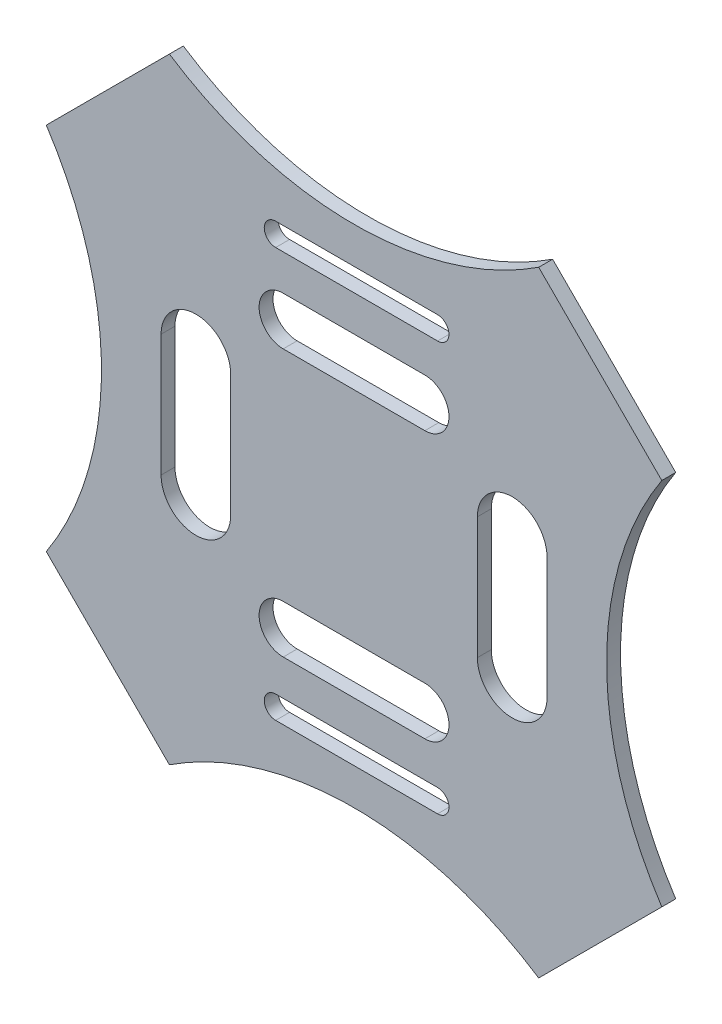
SolidWorks part; units mm, degrees
material "A-Glass Fiber"
ref_plane "Front Plane" through (0, 0, 0) normal (0, 0, 1) x (1, 0, 0)
ref_plane "Top Plane" through (0, 0, 0) normal (0, 1, 0) x (1, 0, 0)
ref_plane "Right Plane" through (0, 0, 0) normal (1, 0, 0) x (0, 0, -1)
sketch "Sketch1" plane through (0, 0, 0) normal (0, 0, 1) x (1, 0, 0)
  line L0 (-26.5165, 44.1942) -> (-44.1942, 26.5165)
  line L1 (-44.1942, 44.1942) -> (44.1942, 44.1942)
  line L2 (-44.1942, 44.1942) -> (-44.1942, -44.1942)
  line L3 (-44.1942, -44.1942) -> (44.1942, -44.1942)
  line L4 (44.1942, 44.1942) -> (44.1942, -44.1942)
  line L5 (0, -44.1942) -> (0, 44.1942) construction
  line L6 (44.1942, 0) -> (-44.1942, 0) construction
  line L7 (26.5165, 44.1942) -> (44.1942, 26.5165)
  line L8 (-26.5165, -44.1942) -> (-44.1942, -26.5165)
  line L9 (26.5165, -44.1942) -> (44.1942, -26.5165)
  line L10 (-44.1942, 44.1942) -> (42.0743, -42.0743) construction
  arc A0 (-44.1942, 26.5165) -> (-44.1942, -26.5165) centre (-84.5999, 0) cw
  arc A1 (44.1942, 26.5165) -> (44.1942, -26.5165) centre (84.5999, 0) ccw
  arc A2 (-26.5165, -44.1942) -> (26.5165, -44.1942) centre (0, -84.5999) cw
  arc A3 (-26.5165, 44.1942) -> (26.5165, 44.1942) centre (0, 84.5999) ccw
  point P19 (0, 0)
  dimension "D1" = 125
  dimension "D2" = 25
extrude "Boss-Extrude1" add sketch "Sketch1" along normal blind 2 contours A3 L1 L0 L2 A0 L8 L3 A2 L9 L4 A1 L7
sketch "Sketch2" plane through (0, 0, 0) normal (0, 0, -1) x (-1, 0, 0)
  line L0 (-36.2703, 0) -> (36.2703, 0) construction
  line L1 (0, 36.2703) -> (0, -36.2703) construction
  line L2 (-22.7088, -8.7575) -> (-22.7088, 8.7575) construction
  line L3 (-27.7088, -8.7575) -> (-27.7088, 8.7575)
  line L4 (-17.7088, -8.7575) -> (-17.7088, 8.7575)
  line L5 (22.7088, -8.7575) -> (22.7088, 8.7575) construction
  line L6 (27.7088, -8.7575) -> (27.7088, 8.7575)
  line L7 (17.7088, -8.7575) -> (17.7088, 8.7575)
  line L8 (-10.1716, 19.161) -> (10.1716, 19.161) construction
  line L9 (-10.1716, 22.6207) -> (10.1716, 22.6207)
  line L10 (-10.1716, 15.7013) -> (10.1716, 15.7013)
  line L11 (-11.9939, 29.4024) -> (11.2564, 29.4024) construction
  line L12 (-11.9939, 31.0398) -> (11.2564, 31.0398)
  line L13 (-11.9939, 27.765) -> (11.2564, 27.765)
  line L14 (-13.6314, 13.9408) -> (-13.6314, 35.1212) construction
  line L15 (-10.1716, -19.161) -> (10.1716, -19.161) construction
  line L16 (-10.1716, -22.6207) -> (10.1716, -22.6207)
  line L17 (-10.1716, -15.7013) -> (10.1716, -15.7013)
  line L18 (-11.9939, -29.4024) -> (11.2564, -29.4024) construction
  line L19 (-11.9939, -31.0398) -> (11.2564, -31.0398)
  line L20 (-11.9939, -27.765) -> (11.2564, -27.765)
  arc A0 (-44.1942, -26.5165) -> (-44.1942, 26.5165) centre (-84.5999, 0) ccw construction
  arc A1 (44.1942, 26.5165) -> (44.1942, -26.5165) centre (84.5999, 0) ccw construction
  arc A2 (-26.5165, 44.1942) -> (26.5165, 44.1942) centre (0, 84.5999) ccw construction
  arc A3 (26.5165, -44.1942) -> (-26.5165, -44.1942) centre (0, -84.5999) ccw construction
  arc A4 (-27.7088, -8.7575) -> (-17.7088, -8.7575) centre (-22.7088, -8.7575) ccw
  arc A5 (-17.7088, 8.7575) -> (-27.7088, 8.7575) centre (-22.7088, 8.7575) ccw
  arc A6 (27.7088, -8.7575) -> (17.7088, -8.7575) centre (22.7088, -8.7575) cw
  arc A7 (17.7088, 8.7575) -> (27.7088, 8.7575) centre (22.7088, 8.7575) cw
  arc A8 (-10.1716, 22.6207) -> (-10.1716, 15.7013) centre (-10.1716, 19.161) ccw
  arc A9 (10.1716, 15.7013) -> (10.1716, 22.6207) centre (10.1716, 19.161) ccw
  arc A10 (-11.9939, 31.0398) -> (-11.9939, 27.765) centre (-11.9939, 29.4024) ccw
  arc A11 (11.2564, 27.765) -> (11.2564, 31.0398) centre (11.2564, 29.4024) ccw
  arc A12 (-10.1716, -22.6207) -> (-10.1716, -15.7013) centre (-10.1716, -19.161) cw
  arc A13 (10.1716, -15.7013) -> (10.1716, -22.6207) centre (10.1716, -19.161) cw
  arc A14 (-11.9939, -31.0398) -> (-11.9939, -27.765) centre (-11.9939, -29.4024) cw
  arc A15 (11.2564, -27.765) -> (11.2564, -31.0398) centre (11.2564, -29.4024) cw
  point P18 (-22.7088, 0)
  point P25 (22.7088, 0)
  point P32 (0, 19.161)
  point P39 (-0.3688, 29.4024)
  point P48 (0, -19.161)
  point P55 (-0.3688, -29.4024)
  dimension "D1" = 5
extrude "Cut-Extrude1" cut sketch "Sketch2" against normal blind 10
sketch "Sketch3" plane through (0, 0, 0) normal (0, 0, -1) x (-1, 0, 0)
  line L0 (-35.3553, 35.3553) -> (35.3553, -35.3553) construction
  line L1 (-26.5165, 44.1942) -> (-44.1942, 26.5165) construction
  line L2 (26.5165, -44.1942) -> (44.1942, -26.5165) construction
  line L3 (-36.2703, 0) -> (36.2703, 0) construction
  line L6 (0, 36.2703) -> (0, -36.2703) construction
  circle A0 centre (-37.897, 23.6195) radius 2.1225
  circle A1 centre (-23.6195, 37.897) radius 2.1225
  circle A2 centre (-24.7033, 18.3068) radius 2.0097
  circle A3 centre (-18.3068, 24.7033) radius 2.0097
  arc A4 (-44.1942, -26.5165) -> (-44.1942, 26.5165) centre (-84.5999, 0) ccw construction
  arc A5 (44.1942, 26.5165) -> (44.1942, -26.5165) centre (84.5999, 0) ccw construction
  arc A6 (-26.5165, 44.1942) -> (26.5165, 44.1942) centre (0, 84.5999) ccw construction
  arc A7 (26.5165, -44.1942) -> (-26.5165, -44.1942) centre (0, -84.5999) ccw construction
  circle A8 centre (18.3068, 24.7033) radius 2.0097
  circle A9 centre (24.7033, 18.3068) radius 2.0097
  circle A10 centre (23.6195, 37.897) radius 2.1225
  circle A11 centre (37.897, 23.6195) radius 2.1225
  circle A12 centre (37.897, -23.6195) radius 2.1225
  circle A13 centre (23.6195, -37.897) radius 2.1225
  circle A14 centre (24.7033, -18.3068) radius 2.0097
  circle A15 centre (18.3068, -24.7033) radius 2.0097
  circle A16 centre (-18.3068, -24.7033) radius 2.0097
  circle A17 centre (-24.7033, -18.3068) radius 2.0097
  circle A18 centre (-23.6195, -37.897) radius 2.1225
  circle A19 centre (-37.897, -23.6195) radius 2.1225
extrude "Boss-Extrude2" [suppressed] add sketch "Sketch3" along normal blind 1 separate body contours A0 | A2
ref_plane "Plane1" through (0, 0, 0) normal (0.7071, -0.7071, 0) x (-0.7071, -0.7071, 0)
fillet "Fillet1" [suppressed] radius 0.5
fillet "Fillet2" [suppressed] radius 0.6
fillet "Fillet3" [suppressed] radius 0.6
mirror "Mirror2" [suppressed] about plane through (0, 0, 0) normal (0.7071, -0.7071, 0)
mirror "Mirror3" [suppressed] about plane through (0, 0, 0) normal (1, 0, 0)
mirror "Mirror4" [suppressed] about plane through (0, 0, 0) normal (0, 1, 0)
